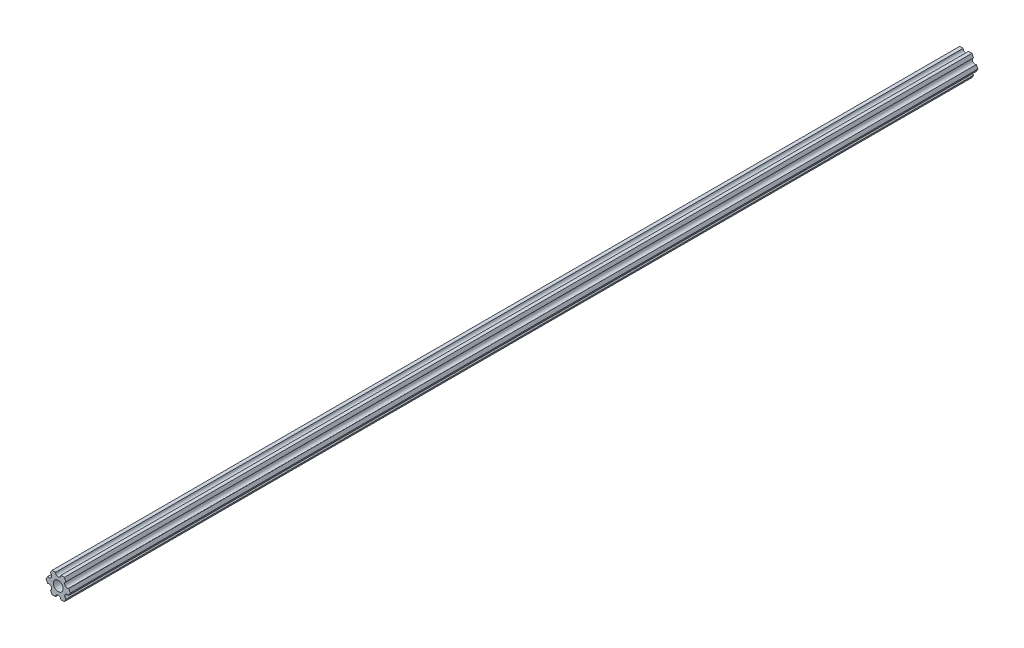
SolidWorks part; units mm, degrees
ref_plane "Front Plane" through (0, 0, 0) normal (0, 0, 1) x (1, 0, 0)
ref_plane "Top Plane" through (0, 0, 0) normal (0, 1, 0) x (1, 0, 0)
ref_plane "Right Plane" through (0, 0, 0) normal (1, 0, 0) x (0, 0, -1)
ref_plane "Plane1" through (0, 0, 0) normal (0, 0, -1) x (-1, 0, 0)
sketch "Sketch1" plane through (0, 0, 0) normal (0, 0, -1) x (-1, 0, 0)
  line L0 (-4.7055, -4.5498) -> (-3.6662, -6.35)
  line L1 (-3.6662, -6.35) -> (-1.5875, -6.35)
  line L2 (1.5875, -6.35) -> (3.6662, -6.35)
  line L3 (3.6662, -6.35) -> (4.7055, -4.5498)
  line L4 (6.293, -1.8002) -> (7.3323, 0)
  line L5 (7.3323, 0) -> (6.293, 1.8002)
  line L6 (4.7055, 4.5498) -> (3.6662, 6.35)
  line L7 (3.6662, 6.35) -> (1.5875, 6.35)
  line L8 (-1.5875, 6.35) -> (-3.6662, 6.35)
  line L9 (-3.6662, 6.35) -> (-4.7055, 4.5498)
  line L10 (-6.293, 1.8002) -> (-7.3323, 0)
  line L11 (-7.3323, 0) -> (-6.293, -1.8002)
  circle A0 centre (0, 0) radius 2.9337
  arc A1 (-6.293, -1.8002) -> (-4.7055, -4.5498) centre (-5.4993, -3.175) cw
  arc A2 (-1.5875, -6.35) -> (1.5875, -6.35) centre (0, -6.35) cw
  arc A3 (4.7055, -4.5498) -> (6.293, -1.8002) centre (5.4993, -3.175) cw
  arc A4 (6.293, 1.8002) -> (4.7055, 4.5498) centre (5.4993, 3.175) cw
  arc A5 (1.5875, 6.35) -> (-1.5875, 6.35) centre (0, 6.35) cw
  arc A6 (-4.7055, 4.5498) -> (-6.293, 1.8002) centre (-5.4993, 3.175) cw
extrude "Boss-Extrude1" add sketch "Sketch1" against normal blind 546.1
